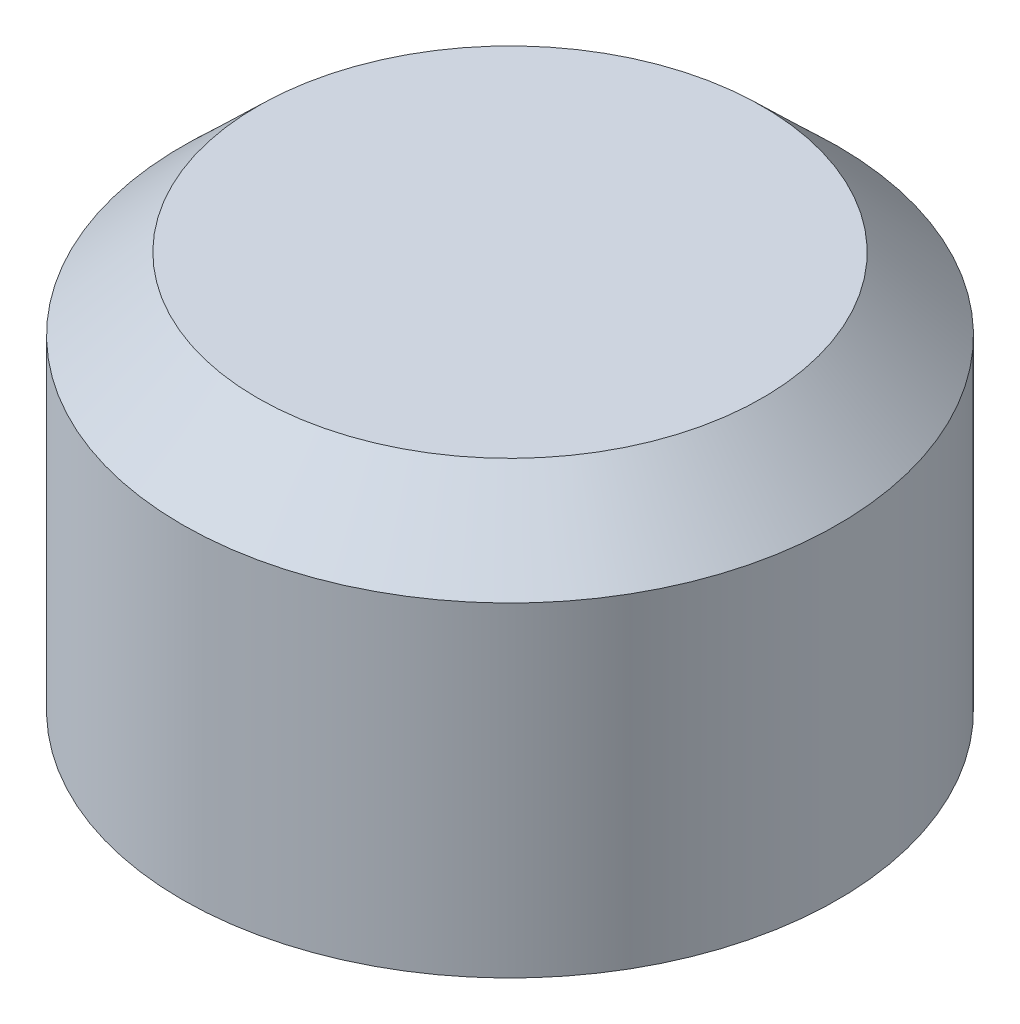
SolidWorks part; units mm, degrees
ref_plane "Front Plane" through (0, 0, 0) normal (0, 0, 1) x (1, 0, 0)
ref_plane "Top Plane" through (0, 0, 0) normal (0, 1, 0) x (1, 0, 0)
ref_plane "Right Plane" through (0, 0, 0) normal (1, 0, 0) x (0, 0, -1)
sketch "Sketch1" plane through (0, 0, 0) normal (0, 0, 1) x (1, 0, 0)
  line L0 (-2438.4, 0) -> (-2438.4, 2753.721)
  line L1 (-2438.4, 2753.721) -> (-2118.721, 3073.4)
  line L2 (-2118.721, 3073.4) -> (-1190.8772, 3073.4)
  line L3 (-1190.8772, 3073.4) -> (-914.4, 2796.9228)
  line L4 (-914.4, 2796.9228) -> (-914.4, 1524)
  line L5 (-914.4, 1524) -> (-939.8, 1524)
  line L6 (-939.8, 1524) -> (-939.8, 2786.4018)
  line L7 (-939.8, 2786.4018) -> (-1201.3982, 3048)
  line L8 (-1201.3982, 3048) -> (-2108.2, 3048)
  line L9 (-2108.2, 3048) -> (-2413, 2743.2)
  line L10 (-2413, 2743.2) -> (-2413, 0)
  line L11 (-2413, 0) -> (-2438.4, 0)
  dimension "D1" = 25.4
  dimension "D2" = 914.4
  dimension "D3" = 2743.2
  dimension "D4" = 304.8
  dimension "D5" = 304.8
  dimension "D6" = 25.4
  dimension "D7" = 25.4
  dimension "D8" = 25.4
  dimension "D9" = 25.4
  dimension "D10" = 1524
  dimension "D11" = 2438.4
sketch "Sketch2" plane through (0, 0, 0) normal (0, 0, 1) x (1, 0, 0)
  line L0 (-2743.2, 0) -> (-2768.6, 0)
  line L1 (-2768.6, 0) -> (-2768.6, 2743.2)
  line L2 (-2743.2, 0) -> (-2743.2, 2732.3741)
  line L3 (-2743.2, 2732.3741) -> (-2123.3813, 3327.4)
  line L4 (-2123.3813, 3327.4) -> (0, 3327.4)
  line L5 (0, 3327.4) -> (0, 3352.8)
  line L6 (0, 3352.8) -> (-2133.6, 3352.8)
  line L7 (-2133.6, 3352.8) -> (-2768.6, 2743.2)
  dimension "D1" = 2743.2
  dimension "D2" = 2133.6
  dimension "D3" = 25.4
  dimension "D4" = 25.4
  dimension "D5" = 304.8
  dimension "D6" = 609.6
  dimension "D7" = 25.4
ref_axis "Axis1" through (0, 3520.44, 0) along (0, -1, 0)
revolve "Revolve1" add sketch "Sketch1" angle 360 about axis through (0, 3520.44, 0) along (0, -1, 0)
revolve "Revolve2" add sketch "Sketch2" angle 360 about axis through (0, 3520.44, 0) along (0, -1, 0)
